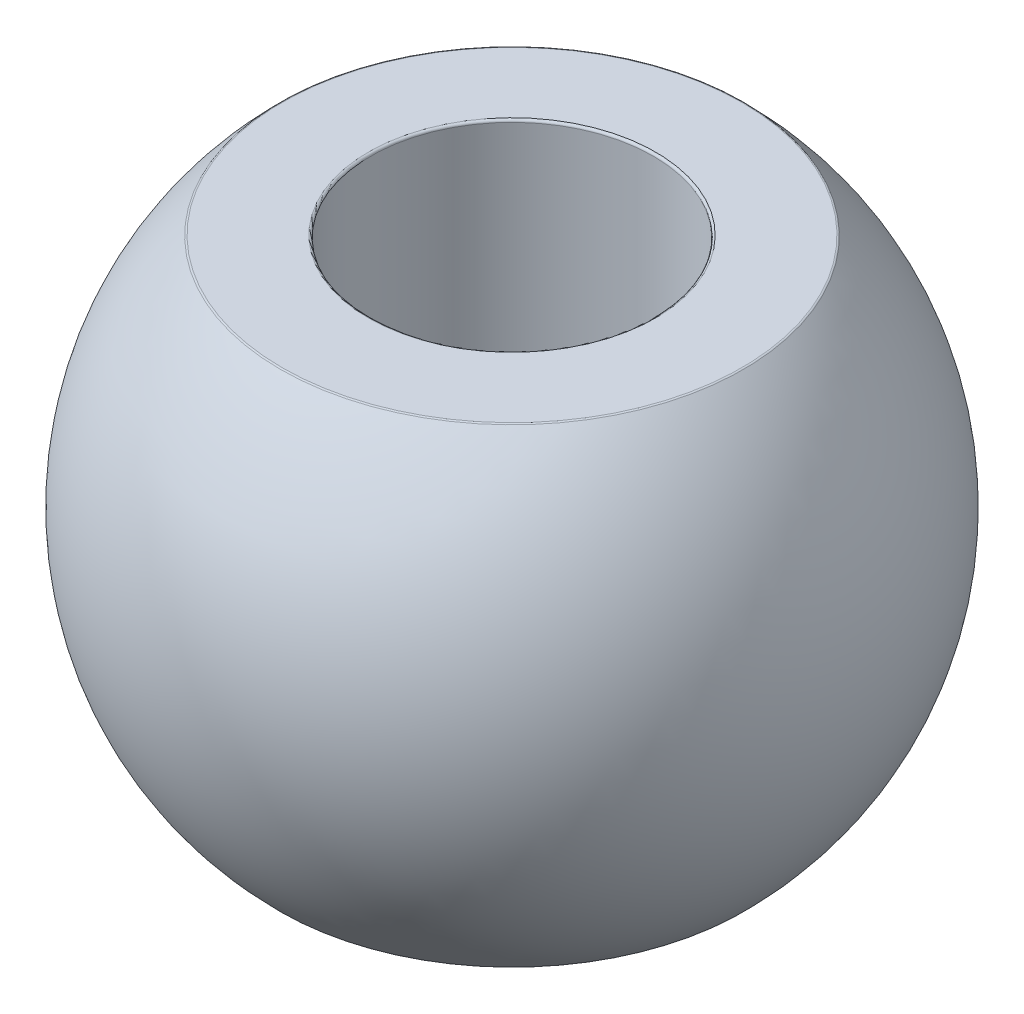
SolidWorks part; units mm, degrees
ref_plane "Front Plane" through (0, 0, 0) normal (0, 0, 1) x (1, 0, 0)
ref_plane "Top Plane" through (0, 0, 0) normal (0, 1, 0) x (1, 0, 0)
ref_plane "Right Plane" through (0, 0, 0) normal (1, 0, 0) x (0, 0, -1)
sketch "Sketch1" plane through (0, 0, 0) normal (0, 0, 1) x (1, 0, 0)
  line L0 (6, 0) -> (0, 0) construction
  line L1 (0, 0) -> (0, 12.58) construction
  line L2 (6, -10) -> (6, 10)
  line L3 (6, 10) -> (9.798, 10)
  line L4 (6, -10) -> (9.798, -10)
  arc A0 (9.798, 10) -> (9.798, -10) centre (0, 0) cw
  dimension "D3" = 14
  dimension "D1" = 6
  dimension "D2" = 20
revolve "Revolve1" add sketch "Sketch1" angle 360 about L1
fillet "Fillet1" radius 0.1 4 edges at (0, -10, -9.798) (0, 10, -9.798) (0, 10, -6) (0, -10, -6)
scale "Scale1" scale about centroid uniform scaling yes scale factor 0.25
